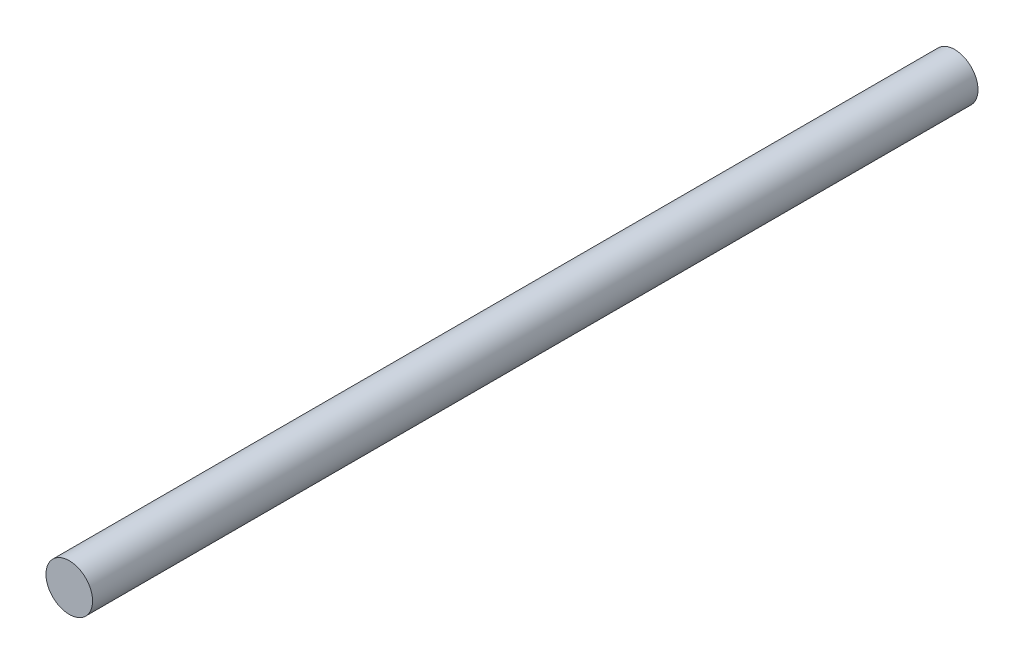
SolidWorks part; units mm, degrees
ref_plane "Front Plane" through (0, 0, 0) normal (0, 0, 1) x (1, 0, 0)
ref_plane "Top Plane" through (0, 0, 0) normal (0, 1, 0) x (1, 0, 0)
ref_plane "Right Plane" through (0, 0, 0) normal (1, 0, 0) x (0, 0, -1)
sketch "Sketch1" plane through (0, 0, 0) normal (0, 0, 1) x (1, 0, 0)
  circle A0 centre (0, 0) radius 1.5
  dimension "D1" = 3
extrude "Boss-Extrude1" add sketch "Sketch1" along normal blind 57
